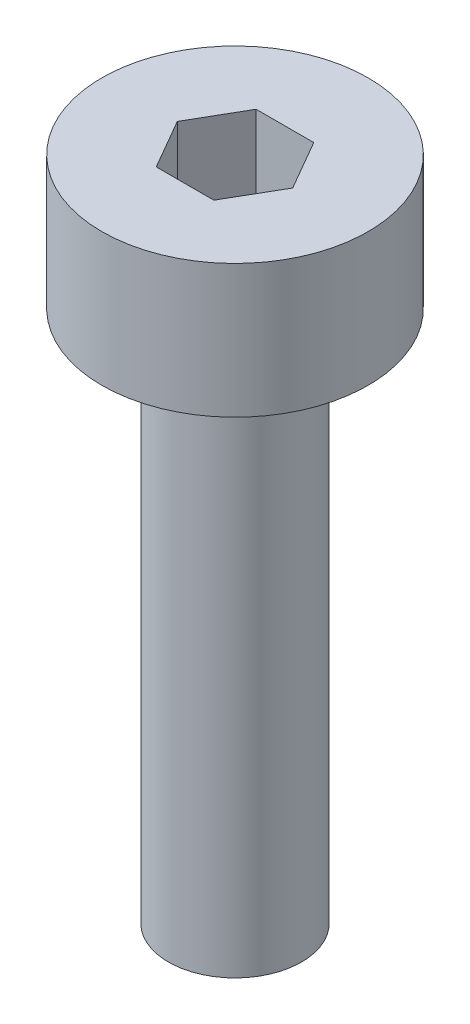
SolidWorks part; units mm, degrees
material "AISI 304"
ref_plane "前视基准面" through (0, 0, 0) normal (0, 0, 1) x (1, 0, 0)
ref_plane "上视基准面" through (0, 0, 0) normal (0, 1, 0) x (1, 0, 0)
ref_plane "右视基准面" through (0, 0, 0) normal (1, 0, 0) x (0, 0, -1)
sketch "草图1" plane through (0, 0, 0) normal (0, 1, 0) x (1, 0, 0)
  circle A0 centre (0, 0) radius 2
  dimension "D1" = 4
extrude "杯头高度" add sketch "草图1" along normal blind 2
sketch "草图2" plane through (0, 2, 0) normal (0, 1, 0) x (1, 0, 0)
  line L1 (0.866, 0) -> (0.433, 0.75)
  line L2 (0.433, 0.75) -> (-0.433, 0.75)
  line L3 (-0.433, 0.75) -> (-0.866, 0)
  line L4 (-0.866, 0) -> (-0.433, -0.75)
  line L5 (-0.433, -0.75) -> (0.433, -0.75)
  line L6 (0.433, -0.75) -> (0.866, 0)
  circle A0 centre (0, 0) radius 0.75 construction
  dimension "D1" = 1.5
extrude "内六角深度" cut sketch "草图2" against normal blind 1.5
sketch "草图3" plane through (0, 0, 0) normal (0, -1, 0) x (1, 0, 0)
  circle A0 centre (0, 0) radius 1
  dimension "D1" = 2
extrude "螺纹长度" add sketch "草图3" along normal blind 8
